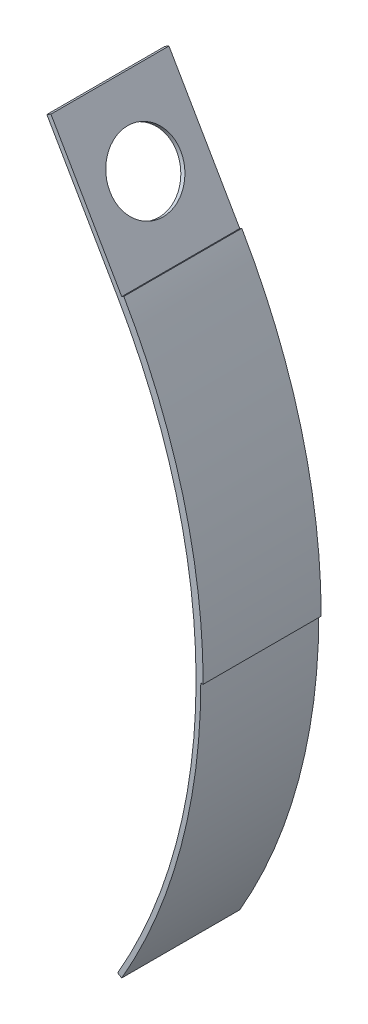
SolidWorks part; units mm, degrees
ref_plane "前视基准面" through (0, 0, 0) normal (0, 0, 1) x (1, 0, 0)
ref_plane "上视基准面" through (0, 0, 0) normal (0, 1, 0) x (1, 0, 0)
ref_plane "右视基准面" through (0, 0, 0) normal (1, 0, 0) x (0, 0, -1)
sketch "草图1" plane through (0, 0, 0) normal (0, 0, 1) x (1, 0, 0)
  line L0 (0, 0) -> (0, -25) construction
  line L1 (0, 0) -> (-3, 5.1962)
  arc A0 (0, 0) -> (0, -25) centre (-21.6506, -12.5) cw
  dimension "D1" = 25
  dimension "D2" = 25
  dimension "D3" = 6
extrude "拉伸-薄壁1" add sketch "草图1" along normal blind 5 thin thin type one direction wall 0.2
sketch "草图2" plane through (-0.1732, -0.1, 0) normal (-0.866, -0.5, 0) x (0, 0, 1)
  line L0 (0, 3) -> (5, 3) construction
  line L1 (0, 6) -> (0, 0) construction
  line L2 (5, 6) -> (5, 0) construction
  line L3 (2.5, 6) -> (2.5, 0) construction
  line L4 (5, 6) -> (0, 6) construction
  line L5 (5, 0) -> (0, 0) construction
  circle A0 centre (2.5, 3) radius 1.5
  dimension "D1" = 3
extrude "切除-拉伸1" cut sketch "草图2" against normal through all
sketch "草图3" plane through (0, 0, 0) normal (0, 0, 1) x (1, 0, 0)
  arc A0 (0, 0) -> (3.3494, -12.5) centre (-21.6506, -12.5) cw
  arc A1 (0, -25) -> (0, 0) centre (-21.6506, -12.5) ccw construction
extrude "拉伸-薄壁2" add sketch "草图3" along normal blind 5 thin thin type one direction reverse wall 0.1
